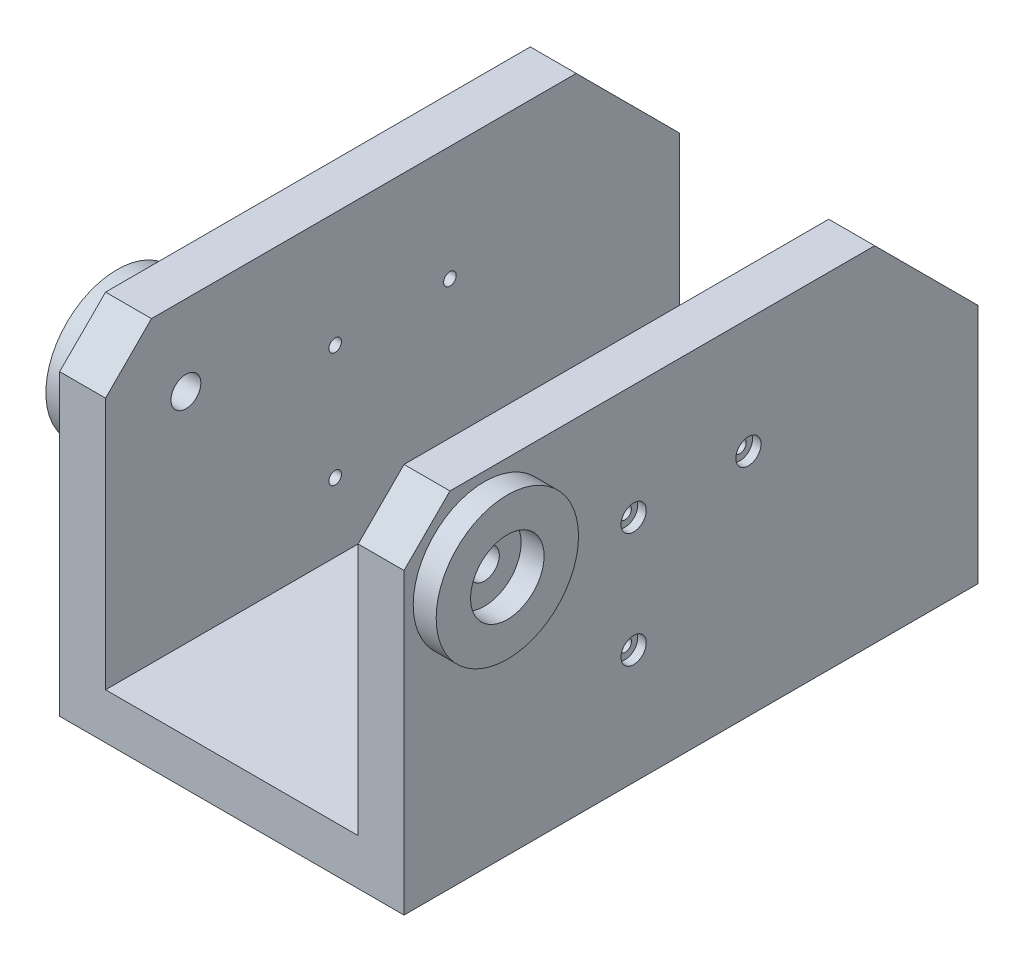
SolidWorks part; units mm, degrees
ref_plane "Alzado" through (0, 0, 0) normal (0, 0, 1) x (1, 0, 0)
ref_plane "Planta" through (0, 0, 0) normal (0, 1, 0) x (1, 0, 0)
ref_plane "Vista lateral" through (0, 0, 0) normal (1, 0, 0) x (0, 0, -1)
sketch "Croquis1" plane through (0, 0, 0) normal (0, 0, 1) x (1, 0, 0)
  line L0 (-55, 130) -> (-55, 0)
  line L1 (-55, 0) -> (55, 0)
  line L2 (55, 0) -> (55, 130)
  line L3 (-75, 130) -> (-75, -20)
  line L4 (-75, -20) -> (75, -20)
  line L5 (75, -20) -> (75, 130)
  line L6 (-75, 130) -> (-55, 130)
  line L7 (55, 130) -> (75, 130)
  point P2 (0, 0)
  dimension "D2" = 150
  dimension "D3" = 110
  dimension "D1" = 20
extrude "Saliente-Extruir1" add sketch "Croquis1" along normal mid plane 250
sketch "Croquis2" plane through (75, 0, 0) normal (1, 0, 0) x (0, 0, -1)
  line L0 (-125, 130) -> (125, 130) construction
  line L1 (-125, -20) -> (-125, 130) construction
  circle A0 centre (-90, 95) radius 16
  circle A1 centre (-90, 95) radius 31
  dimension "D3" = 32
  dimension "D1" = 35
  dimension "D2" = 35
  dimension "D4" = 15
extrude "Saliente-Extruir2" add sketch "Croquis2" along normal blind 10
mirror "Simetría1" about plane through (0, 0, 0) normal (1, 0, 0) of "Saliente-Extruir2"
sketch "Croquis4" plane through (75, 0, 0) normal (1, 0, 0) x (0, 0, -1)
  circle A0 centre (-90, 95) radius 6.5
  dimension "D1" = 13
extrude "Cortar-Extruir2" cut sketch "Croquis4" against normal through all
chamfer "Chaflán2" distance 20 angle 45 2 edges at (65, 130, 125) (-65, 130, 125)
chamfer "Chaflán3" distance 45 angle 45 2 edges at (65, 130, -125) (-65, 130, -125)
sketch "Croquis5" plane through (75, 0, 0) normal (1, 0, 0) x (0, 0, -1)
  line L0 (-105, 130) -> (80, 130) construction
  line L1 (-125, -20) -> (-125, 110) construction
  point P0 (-25, 80)
  point P1 (25, 80)
  point P2 (-25, 30)
  dimension "D1" = 50
  dimension "D2" = 50
  dimension "D3" = 50
  dimension "D4" = 100
hole_wizard "Refrentado para tornillo con cabeza troncocónica de M51" positions "Croquis3D1" profile "Croquis6" counterbore size "M5" standard "Ansi Metric" end condition through all
sketch3d "Croquis3D1"
  point P0 (75, 80, 25)
  point P3 (75, 80, -25)
  point P6 (75, 30, 25)
sketch "Croquis6" plane through (75, 80, 25) normal (0, 1, 0) x (0, 0, -1)
  line L0 (0, 0) -> (0, 160)
  line L1 (0, 160) -> (2.75, 160)
  line L3 (2.75, 160) -> (2.75, 3.7)
  line L4 (2.75, 3.7) -> (5.5, 3.7)
  line L5 (5.5, 3.7) -> (5.5, 0)
  line L7 (5.5, 0) -> (0, 0)
  line L11 (0, -6.35) -> (0, 107.95) construction
  dimension "Diámetro de taladro hasta el siguiente" = 5.5
  dimension "Profundidad de taladro hasta el siguiente" = 160
  dimension "Diámetro de refrentado" = 11
  dimension "Profundidad de refrentado" = 3.7
